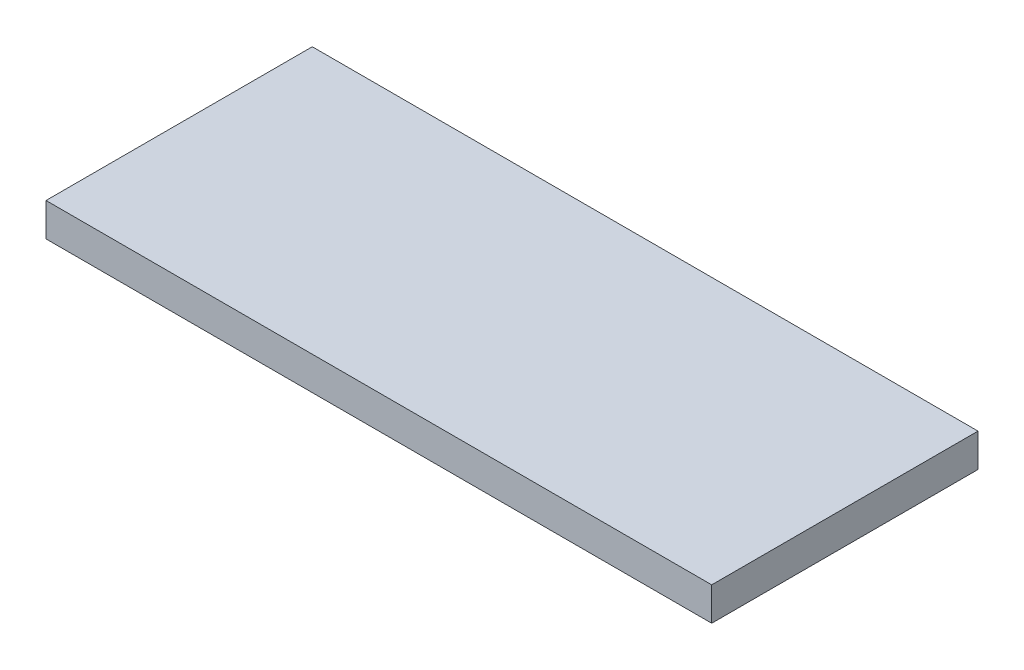
SolidWorks part; units mm, degrees
material "PEI"
ref_plane "Front Plane" through (0, 0, 0) normal (0, 0, 1) x (1, 0, 0)
ref_plane "Top Plane" through (0, 0, 0) normal (0, 1, 0) x (1, 0, 0)
ref_plane "Right Plane" through (0, 0, 0) normal (1, 0, 0) x (0, 0, -1)
sketch "Sketch1" plane through (0, 0, 0) normal (0, 1, 0) x (1, 0, 0)
  line L1 (40, -16) -> (-40, -16)
  line L2 (40, -16) -> (40, 16)
  line L3 (40, 16) -> (-40, 16)
  line L4 (-40, -16) -> (-40, 16)
  line L5 (40, -16) -> (-40, 16) construction
  line L6 (40, 16) -> (-40, -16) construction
  point P0 (0, 0)
  dimension "D1" = 80
  dimension "D2" = 32
extrude "Boss-Extrude1" add sketch "Sketch1" along normal blind 4
